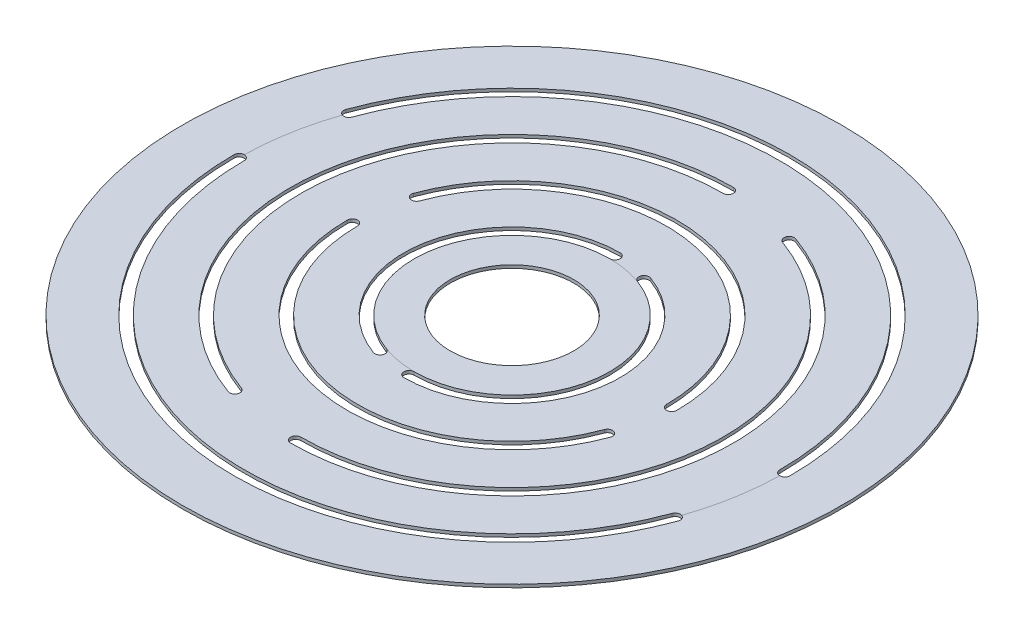
SolidWorks part; units mm, degrees
ref_plane "Front Plane" through (0, 0, 0) normal (0, 0, 1) x (1, 0, 0)
ref_plane "Top Plane" through (0, 0, 0) normal (0, 1, 0) x (1, 0, 0)
ref_plane "Right Plane" through (0, 0, 0) normal (1, 0, 0) x (0, 0, -1)
sketch "Sketch1" plane through (0, 0, 0) normal (0, 1, 0) x (1, 0, 0)
  line L0 (0, 32) -> (0, -32) construction
  line L1 (-32, 0) -> (32, 0) construction
  line L2 (-10.9446, -30.0702) -> (10.9446, 30.0702) construction
  line L3 (30.0702, -10.9446) -> (-30.0702, 10.9446) construction
  circle A0 centre (0, 0) radius 32
  circle A1 centre (0, 0) radius 6
  arc A2 (0, 10) -> (-3.4202, -9.3969) centre (0, 0) ccw
  arc A3 (-15.5, 0) -> (14.5652, -5.3013) centre (0, 0) ccw
  arc A4 (0, 21) -> (-7.1824, -19.7335) centre (0, 0) ccw
  arc A5 (-26.5, 0) -> (24.9019, -9.0635) centre (0, 0) ccw
  arc A8 (26.5, 0) -> (-24.9019, 9.0635) centre (0, 0) ccw
  arc A9 (15.5, 0) -> (-14.5652, 5.3013) centre (0, 0) ccw
  arc A11 (0, -21) -> (7.1824, 19.7335) centre (0, 0) ccw
  arc A12 (0, -10) -> (3.4202, 9.3969) centre (0, 0) ccw
  arc A14 (27, 0) -> (-25.3717, 9.2345) centre (0, 0) ccw
  arc A16 (0, 21.5) -> (-7.3534, -20.2034) centre (0, 0) ccw
  arc A17 (16, 0) -> (-15.0351, 5.4723) centre (0, 0) ccw
  arc A18 (0, -21.5) -> (7.3534, 20.2034) centre (0, 0) ccw
  arc A19 (0, 10.5) -> (-3.5912, -9.8668) centre (0, 0) ccw
  arc A20 (0, -10.5) -> (3.5912, 9.8668) centre (0, 0) ccw
  arc A21 (-16, 0) -> (15.0351, -5.4723) centre (0, 0) ccw
  arc A22 (-27, 0) -> (25.3717, -9.2345) centre (0, 0) ccw
  arc A24 (26, 0) -> (-24.432, 8.8925) centre (0, 0) ccw
  arc A26 (0, 20.5) -> (-7.0114, -19.2637) centre (0, 0) ccw
  arc A27 (15, 0) -> (-14.0954, 5.1303) centre (0, 0) ccw
  arc A28 (0, -20.5) -> (7.0114, 19.2637) centre (0, 0) ccw
  arc A29 (0, 9.5) -> (-3.2492, -8.9271) centre (0, 0) ccw
  arc A30 (0, -9.5) -> (3.2492, 8.9271) centre (0, 0) ccw
  arc A31 (-15, 0) -> (14.0954, -5.1303) centre (0, 0) ccw
  arc A32 (-26, 0) -> (24.432, -8.8925) centre (0, 0) ccw
  arc A35 (27, 0) -> (26, 0) centre (26.5, 0) cw
  arc A36 (-25.3717, 9.2345) -> (-24.432, 8.8925) centre (-24.9019, 9.0635) ccw
  arc A39 (0, 21.5) -> (0, 20.5) centre (0, 21) cw
  arc A40 (-7.3534, -20.2034) -> (-7.0114, -19.2637) centre (-7.1824, -19.7335) ccw
  arc A41 (16, 0) -> (15, 0) centre (15.5, 0) cw
  arc A42 (-15.0351, 5.4723) -> (-14.0954, 5.1303) centre (-14.5652, 5.3013) ccw
  arc A43 (0, -21.5) -> (0, -20.5) centre (0, -21) cw
  arc A44 (7.3534, 20.2034) -> (7.0114, 19.2637) centre (7.1824, 19.7335) ccw
  arc A45 (0, 10.5) -> (0, 9.5) centre (0, 10) cw
  arc A46 (-3.5912, -9.8668) -> (-3.2492, -8.9271) centre (-3.4202, -9.3969) ccw
  arc A47 (0, -10.5) -> (0, -9.5) centre (0, -10) cw
  arc A48 (3.5912, 9.8668) -> (3.2492, 8.9271) centre (3.4202, 9.3969) ccw
  arc A49 (-16, 0) -> (-15, 0) centre (-15.5, 0) cw
  arc A50 (15.0351, -5.4723) -> (14.0954, -5.1303) centre (14.5652, -5.3013) ccw
  arc A51 (-27, 0) -> (-26, 0) centre (-26.5, 0) cw
  arc A52 (25.3717, -9.2345) -> (24.432, -8.8925) centre (24.9019, -9.0635) ccw
  dimension "D1" = 64
  dimension "D2" = 12
  dimension "D3" = 20
  dimension "D4" = 31
  dimension "D5" = 42
  dimension "D6" = 53
  dimension "D8" = 20
  dimension "D9" = 20
  dimension "D10" = 0.5
  dimension "D11" = 0.5
extrude "Boss-Extrude1" add sketch "Sketch1" along normal blind 0.3
sketch "Sketch2" plane through (0, 0.3, 0) normal (0, 1, 0) x (1, 0, 0)
  circle A0 centre (0, 0) radius 9.5
  circle A1 centre (0, 0) radius 26.5
split line "Split Line1"
